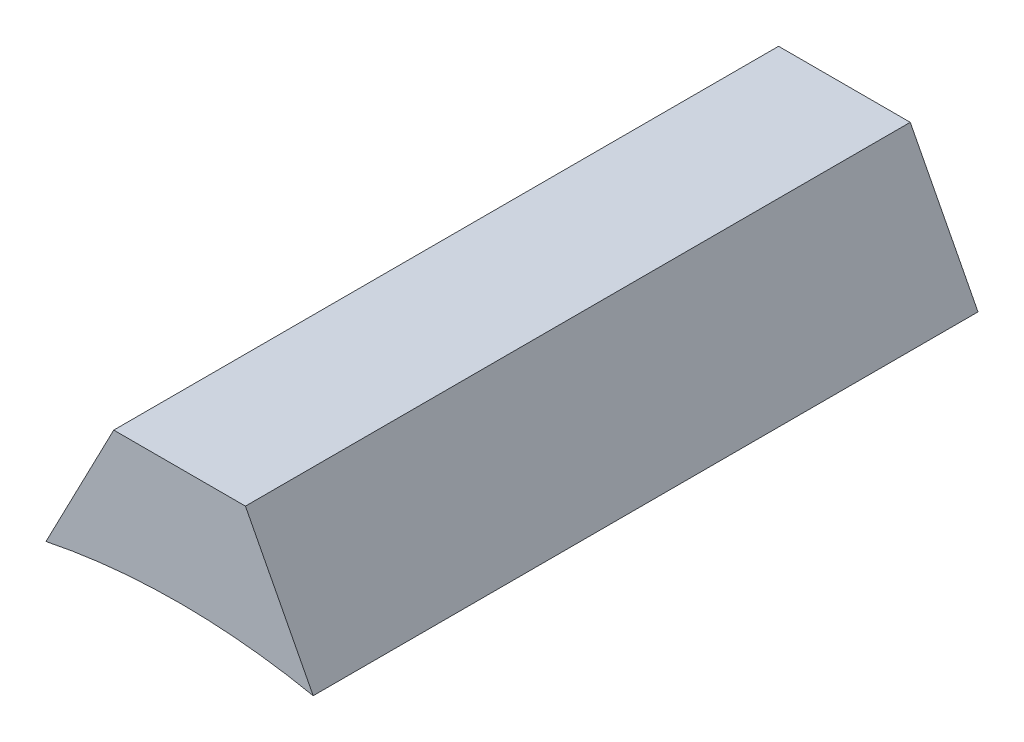
SolidWorks part; units mm, degrees
ref_plane "Front Plane" through (0, 0, 0) normal (0, 0, 1) x (1, 0, 0)
ref_plane "Top Plane" through (0, 0, 0) normal (0, 1, 0) x (1, 0, 0)
ref_plane "Right Plane" through (0, 0, 0) normal (1, 0, 0) x (0, 0, -1)
sketch "Sketch1" plane through (0, 0, 0) normal (0, 0, 1) x (1, 0, 0)
  line L0 (-0.9904, 11.7566) -> (0.9904, 11.7566)
  line L1 (0, -5.5) -> (0, 5.5) construction
  line L2 (0.9904, 11.7566) -> (2.0096, 9.796)
  line L3 (-0.9904, 11.7566) -> (-2.0096, 9.796)
  circle A0 centre (0, 0) radius 10
  point P10 (0, 11.7566)
extrude "Boss-Extrude2" add sketch "Sketch1" along normal blind 10 contours A0 L2 L0 L3
